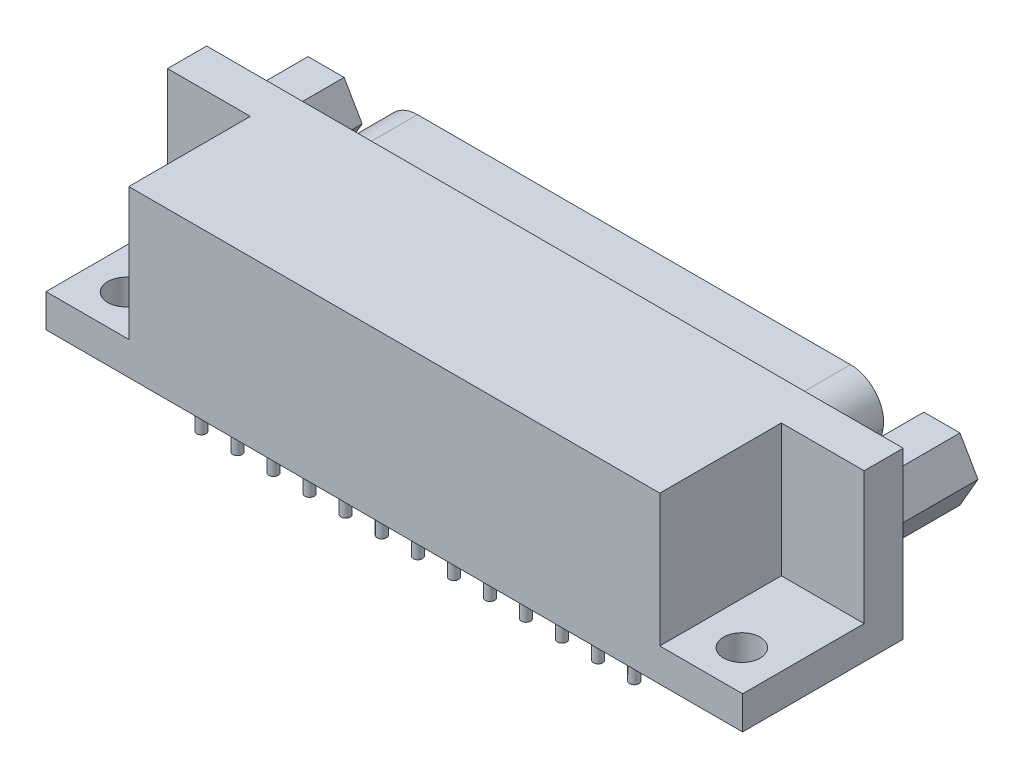
SolidWorks part; units mm, degrees
ref_plane "x/y" through (0, 0, 0) normal (0, 0, 1) x (1, 0, 0)
ref_plane "x/z" through (0, 0, 0) normal (0, 1, 0) x (1, 0, 0)
ref_plane "y/z" through (0, 0, 0) normal (1, 0, 0) x (0, 0, -1)
sketch "Sketch1" plane through (0, 0, 0) normal (0, 1, 0) x (1, 0, 0)
  line L1 (-10.16, -1.77) -> (43.31, -1.77)
  line L2 (-10.16, -1.77) -> (-10.16, 10.56)
  line L3 (-10.16, 10.56) -> (43.31, 10.56)
  line L4 (43.31, -1.77) -> (43.31, 10.56)
  point P3 (16.575, 10.56)
  dimension "D1" = 53.47
  dimension "D2" = 12.33
  dimension "D3" = 1.77
  dimension "D4" = 10.16
extrude "Base-Extrude" add sketch "Sketch1" along normal blind 12.7
sketch "Sketch2" plane through (0, 0, -10.56) normal (0, 0, -1) x (-1, 0, 0)
  line L0 (-16.575, 12.7) -> (-16.575, -6.5379) construction
  line L1 (-43.31, 12.7) -> (10.16, 12.7) construction
  line L2 (-32.6544, 2.286) -> (-0.4956, 2.286)
  line L3 (1.9982, 4.3435) -> (2.5388, 7.1375)
  line L4 (0.045, 10.16) -> (-33.195, 10.16)
  line L6 (-35.1482, 4.3435) -> (-35.6888, 7.1375)
  line L7 (-43.31, 0) -> (10.16, 0) construction
  arc A0 (1.9982, 4.3435) -> (-0.4956, 2.286) centre (-0.4956, 4.826) cw
  arc A1 (0.045, 10.16) -> (2.5388, 7.1375) centre (0.045, 7.62) cw
  arc A2 (-33.195, 10.16) -> (-35.6888, 7.1375) centre (-33.195, 7.62) ccw
  arc A3 (-35.1482, 4.3435) -> (-32.6544, 2.286) centre (-32.6544, 4.826) ccw
  point P4 (-16.575, 10.16)
  point P12 (1.6001, 2.286)
  point P21 (-16.575, 2.286)
  dimension "D5" = 2.54
  dimension "D1" = 2.286
  dimension "D2" = 2.54
  dimension "D3" = 100.95
  dimension "D4" = 33.24
extrude "Boss-Extrude1" add sketch "Sketch2" along normal blind 6.07
sketch "Sketch4" plane through (0, 0, -16.63) normal (0, 0, -1) x (-1, 0, 0)
  line L0 (10.16, 12.7) -> (10.16, 0) construction
  line L2 (-43.31, 12.7) -> (10.16, 12.7) construction
  circle A0 centre (0, 7.62) radius 0.5
  dimension "D1" = 1
  dimension "D2" = 10.16
  dimension "D3" = 5.08
extrude "Cut-Extrude1" cut sketch "Sketch4" against normal blind 5.08
sketch "Sketch5" plane through (0, 0, -16.63) normal (0, 0, -1) x (-1, 0, 0)
  line L0 (10.16, 12.7) -> (10.16, 0) construction
  line L2 (-43.31, 0) -> (10.16, 0) construction
  circle A0 centre (-1.397, 5.08) radius 0.5
  circle A1 centre (0, 7.62) radius 0.5 construction
  dimension "D2" = 5.08
  dimension "D1" = 11.557
extrude "Cut-Extrude2" cut sketch "Sketch5" against normal blind 5.08
sketch "Sketch6" plane through (0, 0, 0) normal (0, -1, 0) x (1, 0, 0)
  circle A0 centre (0, 0) radius 0.3556
  dimension "D1" = 0.7112
extrude "Boss-Extrude2" add sketch "Sketch6" along normal blind 2.54
pattern_linear "LPattern1" count 13 spacing 2.7686 along (1, 0, 0) of "Boss-Extrude2"
pattern_linear "LPattern2" count 13 spacing 2.7686 along (1, 0, 0) of "Cut-Extrude1"
pattern_linear "LPattern3" count 12 spacing 2.7686 along (1, 0, 0) of "Cut-Extrude2"
sketch "Sketch7" plane through (0, 0, 0) normal (0, -1, 0) x (1, 0, 0)
  line L1 (-10.16, -10.56) -> (-10.16, 1.77) construction
  circle A0 centre (1.397, -2.54) radius 0.3556
  dimension "D1" = 0.7112
  dimension "D2" = 11.557
  dimension "D3" = 2.54
extrude "Boss-Extrude3" add sketch "Sketch7" along normal up to surface (2.54 mm away) up to face at (0, -2.54, -0.3556)
pattern_linear "LPattern4" count 12 spacing 2.7686 along (1, 0, 0) of "Boss-Extrude3"
ref_plane "Plane1" through (16.575, 0, 0) normal (1, 0, 0) x (0, 0, -1)
sketch "Sketch12" plane through (0, 0, -10.56) normal (0, 0, -1) x (-1, 0, 0)
  line L0 (-43.31, 12.7) -> (10.16, 12.7) construction
  line L1 (-41.595, 9.82) -> (-42.98, 7.4211)
  line L2 (-42.98, 7.4211) -> (-41.595, 5.0222)
  line L3 (-41.595, 5.0222) -> (-38.825, 5.0222)
  line L4 (-38.825, 5.0222) -> (-37.44, 7.4211)
  line L5 (-37.44, 7.4211) -> (-38.825, 9.82)
  line L6 (-38.825, 9.82) -> (-41.595, 9.82)
  line L7 (-43.31, 12.7) -> (-43.31, 0) construction
  circle A0 centre (-40.21, 7.4211) radius 2.3989 construction
  circle A1 centre (-40.21, 7.4211) radius 1.3043
  dimension "D1" = 2.77
  dimension "D2" = 2.88
  dimension "D3" = 0.33
extrude "Boss-Extrude4" add sketch "Sketch12" along normal blind 6.07
sketch "Sketch9" plane through (0, 0, 1.77) normal (0, 0, 1) x (1, 0, 0)
  line L1 (-10.16, 12.7) -> (-3.8049, 12.7)
  line L2 (-10.16, 12.7) -> (-10.16, 2.54)
  line L3 (-10.16, 2.54) -> (-3.8049, 2.54)
  line L4 (-3.8049, 12.7) -> (-3.8049, 2.54)
  dimension "D1" = 10.16
  dimension "D2" = 6.3551
extrude "Cut-Extrude3" cut sketch "Sketch9" against normal blind 9.33
sketch "Sketch11" plane through (0, 2.54, 0) normal (0, 1, 0) x (-1, 0, 0)
  line L0 (10.16, 1.77) -> (3.8049, 1.77) construction
  line L1 (10.16, -7.56) -> (10.16, 1.77) construction
  circle A0 centre (7.06, -1.27) radius 1.4
  point P2 (6.9825, 1.77)
  dimension "D1" = 2.8
  dimension "D2" = 3.04
  dimension "D3" = 3.1
extrude "Cut-Extrude4" cut sketch "Sketch11" against normal through all
mirror "Mirror1" about plane through (16.575, 0, 0) normal (1, 0, 0) of "Boss-Extrude4", "Cut-Extrude3", "Cut-Extrude4"
sketch "Sketch13" plane through (0, 0, -16.63) normal (0, 0, -1) x (-1, 0, 0)
  line L8 (1.5073, 4.4385) -> (2.0479, 7.2325)
  line L9 (0.045, 9.66) -> (-33.195, 9.66)
  line L10 (-35.1979, 7.2325) -> (-34.6573, 4.4385)
  line L11 (-32.6544, 2.786) -> (-0.4956, 2.786)
  line L12 (1.5073, 4.4385) -> (2.0479, 7.2325)
  line L13 (0.045, 9.66) -> (-33.195, 9.66)
  line L14 (-35.1979, 7.2325) -> (-34.6573, 4.4385)
  line L15 (-32.6544, 2.786) -> (-0.4956, 2.786)
  arc A8 (-0.4956, 2.786) -> (1.5073, 4.4385) centre (-0.4956, 4.826) ccw
  arc A9 (2.0479, 7.2325) -> (0.045, 9.66) centre (0.045, 7.62) ccw
  arc A10 (-33.195, 9.66) -> (-35.1979, 7.2325) centre (-33.195, 7.62) ccw
  arc A11 (-34.6573, 4.4385) -> (-32.6544, 2.786) centre (-32.6544, 4.826) ccw
  arc A12 (-0.4956, 2.786) -> (1.5073, 4.4385) centre (-0.4956, 4.826) ccw
  arc A13 (2.0479, 7.2325) -> (0.045, 9.66) centre (0.045, 7.62) ccw
  arc A14 (-33.195, 9.66) -> (-35.1979, 7.2325) centre (-33.195, 7.62) ccw
  arc A15 (-34.6573, 4.4385) -> (-32.6544, 2.786) centre (-32.6544, 4.826) ccw
  dimension "D1" = 0.5
split line "Split Line1"
chamfer "Chamfer1" distance 0.4 angle 45 25 edges at (9.2028, 5.08, -16.63) (6.4342, 5.08, -16.63) (3.6656, 5.08, -16.63) (0.897, 5.08, -16.63) (-0.5, 7.62, -16.63) (2.2686, 7.62, -16.63) (5.0372, 7.62, -16.63) (7.8058, 7.62, -16.63) (10.5744, 7.62, -16.63) (11.9714, 5.08, -16.63) (14.74, 5.08, -16.63) (13.343, 7.62, -16.63) (16.1116, 7.62, -16.63) (17.5086, 5.08, -16.63) (20.2772, 5.08, -16.63) (18.8802, 7.62, -16.63) (21.6488, 7.62, -16.63) (23.0458, 5.08, -16.63) (25.8144, 5.08, -16.63) (24.4174, 7.62, -16.63) (27.186, 7.62, -16.63) (28.583, 5.08, -16.63) (31.3516, 5.08, -16.63) (29.9546, 7.62, -16.63) (32.7232, 7.62, -16.63)
